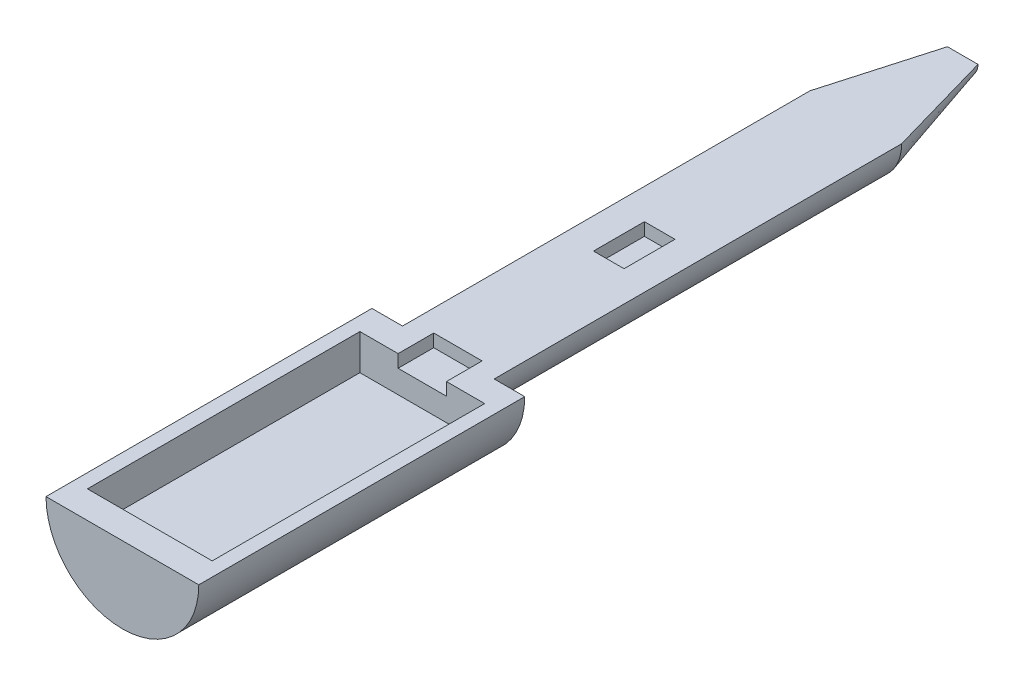
SolidWorks part; units mm, degrees
ref_plane "Front Plane" through (0, 0, 0) normal (0, 0, 1) x (1, 0, 0)
ref_plane "Top Plane" through (0, 0, 0) normal (0, 1, 0) x (1, 0, 0)
ref_plane "Right Plane" through (0, 0, 0) normal (1, 0, 0) x (0, 0, -1)
sketch "Sketch2" plane through (0, 0, 0) normal (0, 1, 0) x (1, 0, 0)
  line L0 (0, 0) -> (-15, 0)
  line L1 (-15, 0) -> (-15, 64)
  line L2 (-15, 64) -> (-9, 64)
  line L3 (-9, 64) -> (-9, 144)
  line L4 (-9, 144) -> (-3, 165)
  line L5 (-3, 165) -> (0, 165)
  line L6 (0, 165) -> (0, 0)
  dimension "D1" = 15
  dimension "D2" = 64
  dimension "D3" = 80
  dimension "D4" = 9
  dimension "D5" = 101
  dimension "D6" = 3
revolve "Revolve1" add sketch "Sketch2" angle 180 about L6
sketch "Sketch3" plane through (0, 0, 0) normal (0, 1, 0) x (1, 0, 0)
  line L0 (-12.25, 5.3825) -> (12.25, 5.3825)
  line L1 (12.25, 5.3825) -> (12.25, 58.8825)
  line L2 (12.25, 58.8825) -> (-12.25, 58.8825)
  line L3 (-12.25, 58.8825) -> (-12.25, 5.3825)
  point P2 (0, 5.3825)
  dimension "D1" = 24.5
  dimension "D2" = 53.5
extrude "Cut-Extrude1" cut sketch "Sketch3" against normal blind 7
sketch "Sketch4" plane through (0, 0, 0) normal (0, 1, 0) x (1, 0, 0)
  line L0 (-4.75, 58.8825) -> (-4.75, 65.8825)
  line L1 (12.25, 58.8825) -> (-12.25, 58.8825) construction
  line L2 (-4.75, 65.8825) -> (4.75, 65.8825)
  line L3 (4.75, 65.8825) -> (4.75, 58.8825)
  line L4 (4.75, 58.8825) -> (-4.75, 58.8825)
  point P4 (0, 58.8825)
  dimension "D1" = 9.5
  dimension "D2" = 7
extrude "Cut-Extrude2" cut sketch "Sketch4" against normal blind 2.5
sketch "Sketch5" plane through (0, 0, 0) normal (0, 1, 0) x (1, 0, 0)
  line L1 (-3, 105.5) -> (3, 105.5)
  line L2 (-3, 105.5) -> (-3, 95.5)
  line L3 (-3, 95.5) -> (3, 95.5)
  line L4 (3, 105.5) -> (3, 95.5)
  point P4 (0, 95.5)
  dimension "D1" = 95.5
  dimension "D2" = 10
  dimension "D3" = 6
extrude "Cut-Extrude3" cut sketch "Sketch5" against normal blind 2.5
